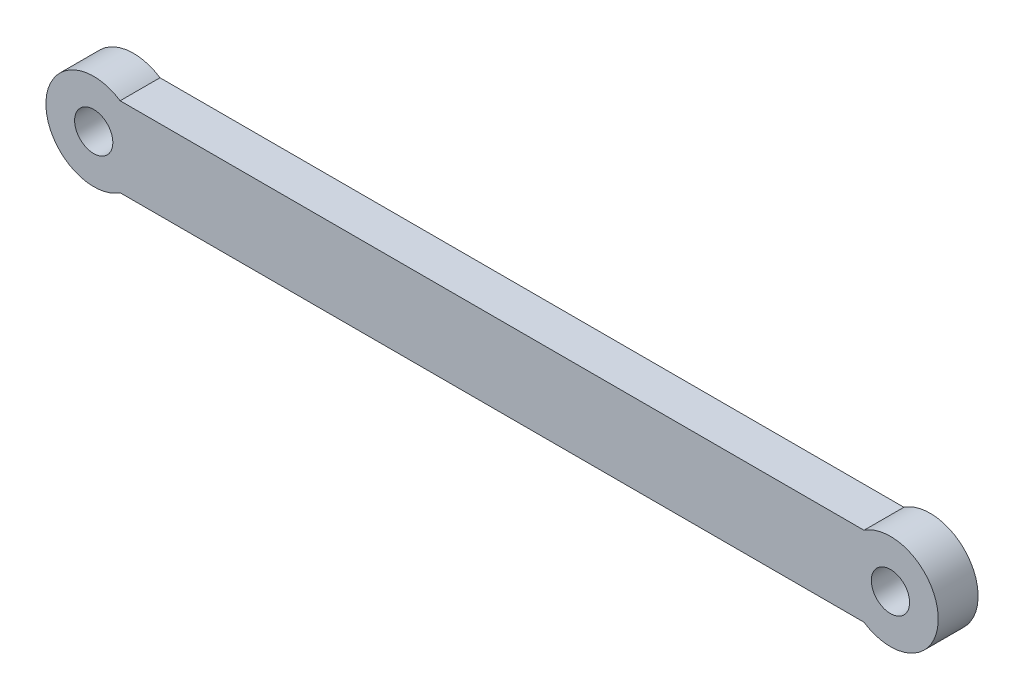
SolidWorks part; units mm, degrees
ref_plane "Front Plane" through (0, 0, 0) normal (0, 0, 1) x (1, 0, 0)
ref_plane "Top Plane" through (0, 0, 0) normal (0, 1, 0) x (1, 0, 0)
ref_plane "Right Plane" through (0, 0, 0) normal (1, 0, 0) x (0, 0, -1)
sketch "Sketch14" plane through (0, 0, 0) normal (0, 0, 1) x (1, 0, 0)
  line L0 (0, 2.5) -> (50, 2.5)
  line L1 (0, -2.5) -> (50, -2.5)
  circle A0 centre (0, 0) radius 1.2
  circle A1 centre (0, 0) radius 2.5
  circle A2 centre (50, 0) radius 1.2
  circle A3 centre (50, 0) radius 2.5
  dimension "D1" = 2.4
  dimension "D2" = 5
  dimension "D3" = 5
  dimension "D4" = 50
extrude "Boss-Extrude1" add sketch "Sketch14" along normal blind 2.5 separate body contours A3 L0 A1 L1 | A3 A2 | A1 A0
sketch "Sketch15" plane through (0, 0, 2.5) normal (0, 0, 1) x (1, 0, 0)
  circle A0 centre (50, 0) radius 3
  circle A1 centre (0, 0) radius 3
  circle A2 centre (0, 0) radius 1.2 construction
  circle A3 centre (50, 0) radius 1.2 construction
  circle A4 centre (0, 0) radius 1.2
  circle A5 centre (50, 0) radius 1.2
  dimension "D1" = 6
extrude "Boss-Extrude2" add sketch "Sketch15" against normal blind 2.5
